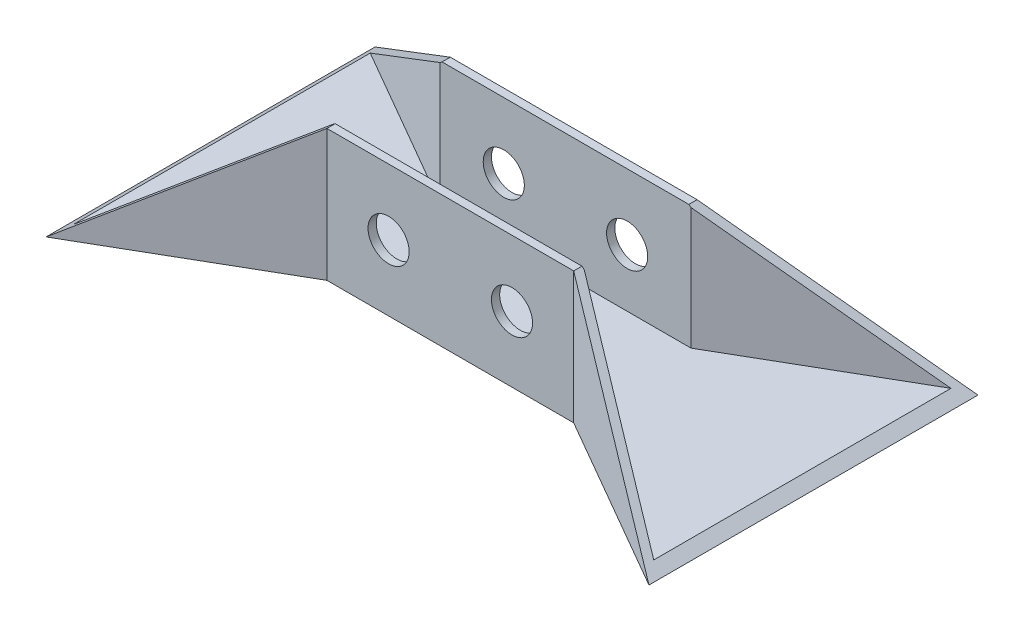
SolidWorks part; units mm, degrees
ref_plane "Front Plane" through (0, 0, 0) normal (0, 0, 1) x (1, 0, 0)
ref_plane "Top Plane" through (0, 0, 0) normal (0, 1, 0) x (1, 0, 0)
ref_plane "Right Plane" through (0, 0, 0) normal (1, 0, 0) x (0, 0, -1)
sketch "Sketch1" plane through (0, 0, 0) normal (0, 1, 0) x (1, 0, 0)
  line L0 (-183.2532, 100) -> (-183.2532, -100)
  line L1 (-183.2532, -100) -> (-75, -37.5)
  line L2 (-75, -37.5) -> (75, -37.5)
  line L3 (75, -37.5) -> (183.2532, -100)
  line L4 (183.2532, -100) -> (183.2532, 100)
  line L5 (183.2532, 100) -> (75, 37.5)
  line L6 (75, 37.5) -> (-75, 37.5)
  line L7 (-75, 37.5) -> (-183.2532, 100)
  line L8 (0, 0) -> (0, 37.5) construction
  line L9 (0, 0) -> (183.2532, 0) construction
  dimension "D1" = 150
  dimension "D2" = 150
  dimension "D3" = 200
  dimension "D4" = 75
extrude "Boss-Extrude1" add sketch "Sketch1" along normal blind 5
sketch "Sketch2" plane through (0, 5, 0) normal (0, 1, 0) x (1, 0, 0)
  line L0 (-183.2532, -100) -> (-75, -37.5)
  line L1 (-75, -37.5) -> (75, -37.5)
  line L2 (75, -37.5) -> (183.2532, -100)
  line L3 (-183.2532, 100) -> (-75, 37.5)
  line L4 (-75, 37.5) -> (75, 37.5)
  line L5 (75, 37.5) -> (183.2532, 100)
  line L6 (-183.2532, 94.2265) -> (-76.3397, 32.5)
  line L7 (-76.3397, 32.5) -> (76.3397, 32.5)
  line L8 (76.3397, 32.5) -> (183.2532, 94.2265)
  line L9 (-183.2532, -94.2265) -> (-76.3397, -32.5)
  line L10 (-76.3397, -32.5) -> (76.3397, -32.5)
  line L11 (76.3397, -32.5) -> (183.2532, -94.2265)
  line L12 (-183.2532, -100) -> (-183.2532, -94.2265)
  line L13 (-183.2532, 100) -> (-183.2532, -100) construction
  line L14 (-185.7532, -95.6699) -> (-76.3397, -32.5) construction
  line L15 (183.2532, -100) -> (183.2532, -94.2265)
  line L16 (183.2532, -100) -> (183.2532, 100) construction
  line L17 (76.3397, -32.5) -> (185.7532, -95.6699) construction
  line L18 (183.2532, 100) -> (183.2532, 94.2265)
  line L19 (76.3397, 32.5) -> (185.7532, 95.6699) construction
  line L20 (-183.2532, 100) -> (-183.2532, 94.2265)
  line L21 (-185.7532, 95.6699) -> (-76.3397, 32.5) construction
  dimension "D1" = 5
  dimension "D2" = 5
extrude "Boss-Extrude2" add sketch "Sketch2" along normal blind 75
sketch "Sketch3" plane through (0, 0, 0) normal (0, 0, 1) x (1, 0, 0)
  line L0 (-183.2532, 0) -> (-75, 80)
  line L1 (-75, 80) -> (-183.2532, 80)
  line L2 (-183.2532, 80) -> (-183.2532, 0)
  line L3 (0, 0) -> (0, 157.2323) construction
  line L4 (-75, 80) -> (75, 80) construction
  line L5 (-75, 80) -> (-75, 0) construction
  line L6 (183.2532, 0) -> (75, 80)
  line L7 (183.2532, 80) -> (183.2532, 0)
  line L8 (75, 80) -> (183.2532, 80)
extrude "Cut-Extrude1" cut sketch "Sketch3" against normal through all both and the other way through all
sketch "Sketch4" plane through (0, 0, 0) normal (0, 0, 1) x (1, 0, 0)
  line L0 (0, 0) -> (0, 80) construction
  line L1 (-75, 80) -> (75, 80) construction
  line L3 (-75, 80) -> (-75, 0) construction
  line L4 (0, 40) -> (-75, 40) construction
  circle A0 centre (-37.5, 40) radius 12.5
  circle A1 centre (37.5, 40) radius 12.5
  dimension "D1" = 25
extrude "Cut-Extrude2" cut sketch "Sketch4" against normal through all both and the other way through all
